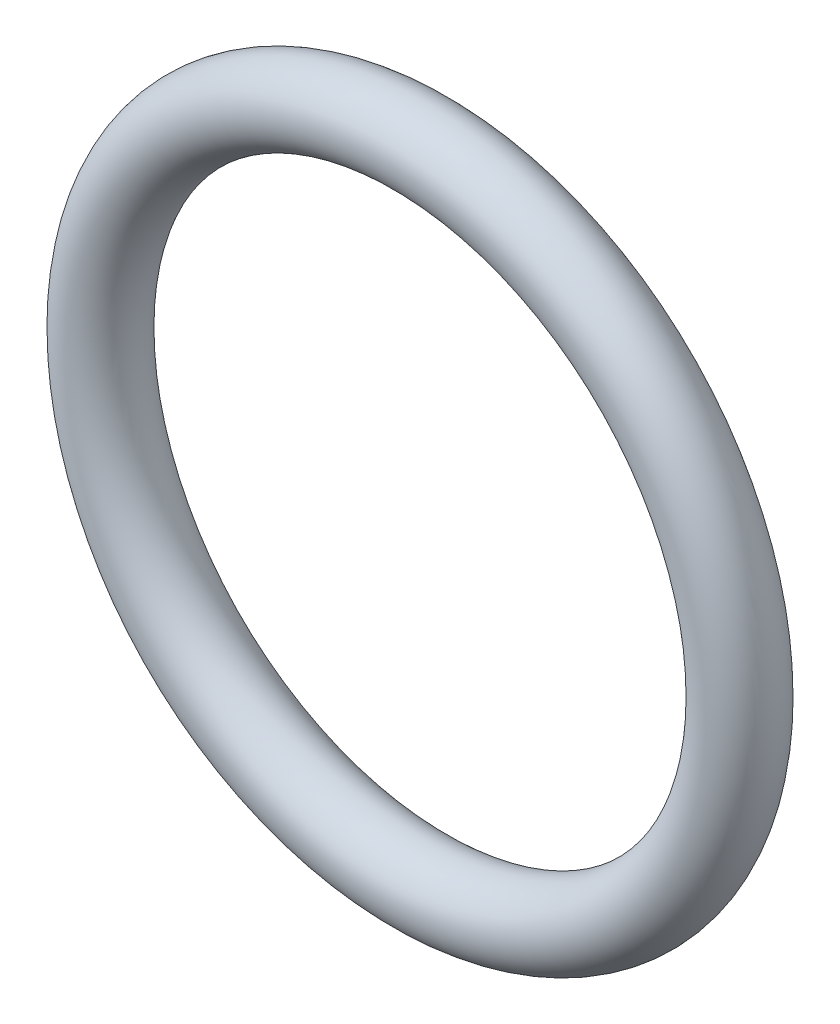
SolidWorks part; units mm, degrees
ref_plane "Plan de face" through (0, 0, 0) normal (0, 0, 1) x (1, 0, 0)
ref_plane "Plan de dessus" through (0, 0, 0) normal (0, 1, 0) x (1, 0, 0)
ref_plane "Plan de droite" through (0, 0, 0) normal (1, 0, 0) x (0, 0, -1)
sketch "Esquisse1" plane through (0, 0, 0) normal (0, 1, 0) x (1, 0, 0)
  line L0 (0, 4.3709) -> (0, 0) construction
  line L1 (0, 0) -> (-7.6, 0) construction
  circle A0 centre (-7.6, 0) radius 0.9
  dimension "D1" = 1.8
  dimension "D2" = 8.5
revolve "Révolution1" add sketch "Esquisse1" angle 360 about L0
sketch "Esquisse2" plane through (0, 0, 0) normal (0, 0, 1) x (1, 0, 0)
  circle A0 centre (0, 0) radius 2.7245
